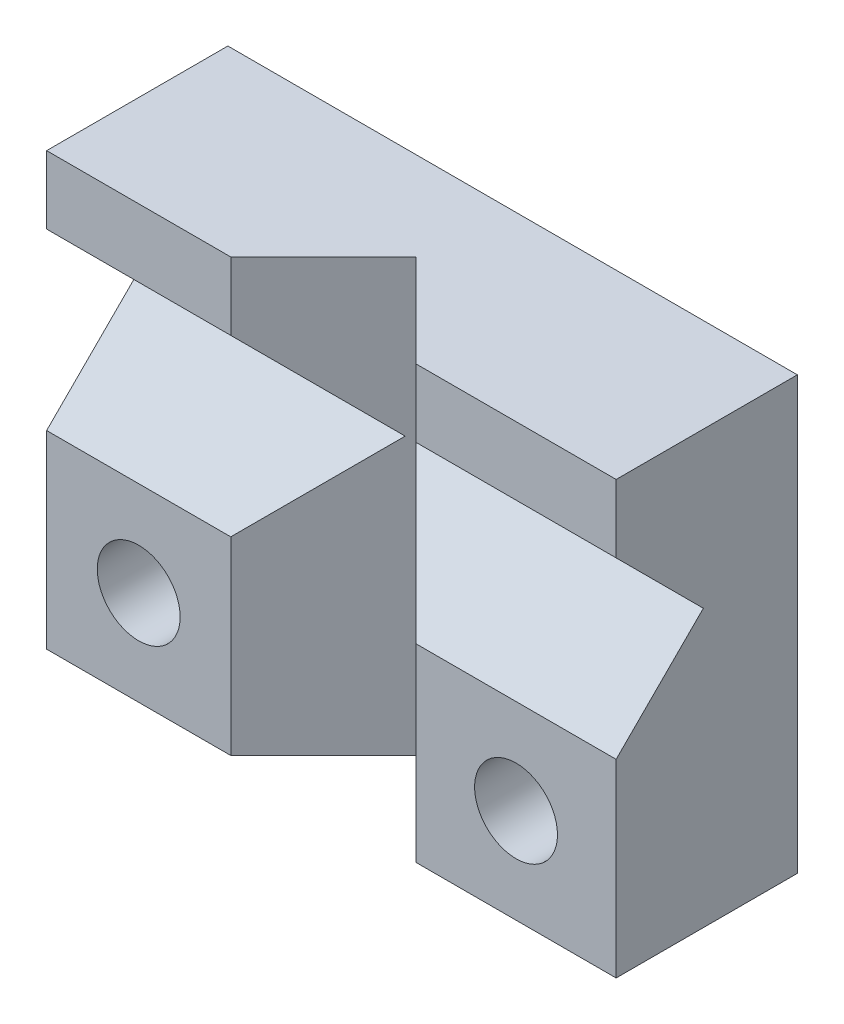
SolidWorks part; units mm, degrees
ref_plane "Front Plane" through (0, 0, 0) normal (0, 0, 1) x (1, 0, 0)
ref_plane "Top Plane" through (0, 0, 0) normal (0, 1, 0) x (1, 0, 0)
ref_plane "Right Plane" through (0, 0, 0) normal (1, 0, 0) x (0, 0, -1)
sketch "Sketch1" plane through (0, 0, 0) normal (0, 0, 1) x (1, 0, 0)
  line L1 (-6.285, 4.765) -> (6.285, 4.765)
  line L2 (-6.285, 4.765) -> (-6.285, -4.765)
  line L3 (-6.285, -4.765) -> (6.285, -4.765)
  line L4 (6.285, 4.765) -> (6.285, -4.765)
  line L5 (-6.285, 4.765) -> (6.285, -4.765) construction
  line L6 (-6.285, -4.765) -> (6.285, 4.765) construction
  point P0 (0, 0)
extrude "Boss-Extrude1" add sketch "Sketch1" along normal blind 4
sketch "Sketch2" plane through (-6.285, 0, 0) normal (-1, 0, 0) x (0, 0, 1)
  line L0 (4, 3.265) -> (4, -0.585)
  line L1 (4, 4.765) -> (4, -4.765) construction
  line L2 (4, 3.265) -> (2.075, 1.34)
  line L3 (2.075, 1.34) -> (4, -0.585)
extrude "Cut-Extrude1" cut sketch "Sketch2" against normal up to next
sketch "Sketch3" plane through (0, 4.765, 0) normal (0, 1, 0) x (1, 0, 0)
  line L1 (6.285, -4) -> (-6.285, -4) construction
  line L2 (-2.221, -4) -> (-0.1773, -1.9563)
  line L3 (-0.1773, -1.9563) -> (1.8663, -4)
  line L5 (-2.221, -4) -> (1.8663, -4)
extrude "Cut-Extrude2" cut sketch "Sketch3" against normal up to next
sketch "Sketch4" plane through (0, 0, 4) normal (0, 0, 1) x (1, 0, 0)
  line L0 (-6.285, -0.585) -> (-2.221, -4.765) construction
  line L1 (-6.285, -4.765) -> (-2.221, -0.585)
  line L2 (-2.221, -0.585) -> (-6.285, -0.585) construction
  line L3 (1.8663, -0.585) -> (6.285, -4.765) construction
  line L4 (1.8663, -4.765) -> (6.285, -0.585) construction
hole_wizard "#1-72 Tapped Hole1" positions "Sketch5" profile "Sketch7" tap size "#1-72" standard "ANSI Inch" end condition up to next
sketch "Sketch5" plane through (0, 0, 4) normal (0, 0, 1) x (1, 0, 0)
  line L0 (-6.285, -4.765) -> (-2.221, -0.585) construction
  line L1 (1.8663, -0.585) -> (6.285, -4.765) construction
  point P0 (-4.253, -2.675)
  point P4 (4.0757, -2.675)
sketch "Sketch7" plane through (-4.253, -2.675, 4) normal (1, 0, 0) x (0, -1, 0)
  line L0 (0, 0) -> (0, 4)
  line L1 (0, 4) -> (0.9144, 4)
  line L2 (0.9144, 4) -> (0.9144, 0)
  line L5 (0.9144, 0) -> (0, 0)
  line L11 (0, -6.35) -> (0, 107.95) construction
  dimension "Thru Tap Drill Dia." = 1.8288
  dimension "Thru Tap Drill Depth" = 4
cosmetic thread "Hole Thread1" parameters "D2"=1.8542
cosmetic thread "Hole Thread2" parameters "D2"=1.8542
